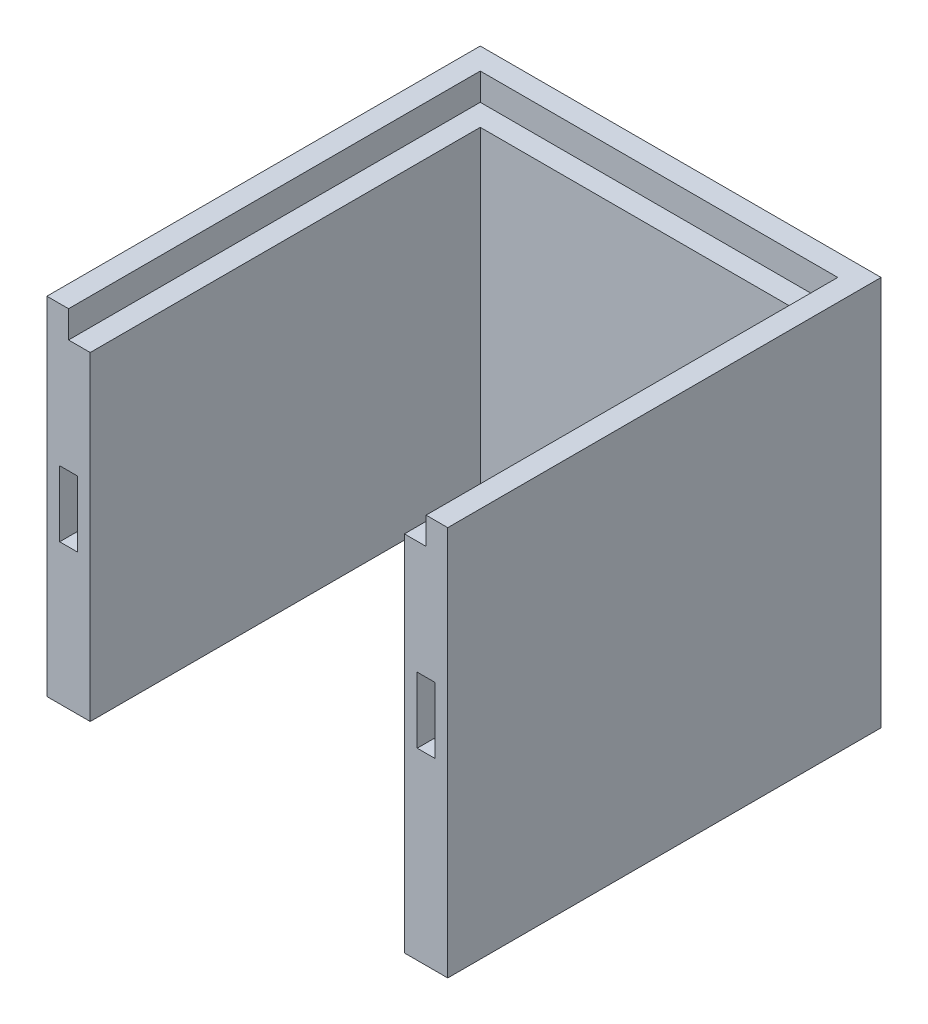
SolidWorks part; units mm, degrees
ref_plane "Front Plane" through (0, 0, 0) normal (0, 0, 1) x (1, 0, 0)
ref_plane "Top Plane" through (0, 0, 0) normal (0, 1, 0) x (1, 0, 0)
ref_plane "Right Plane" through (0, 0, 0) normal (1, 0, 0) x (0, 0, -1)
sketch "Sketch1" plane through (0, 0, 0) normal (0, 0, 1) x (1, 0, 0)
  line L1 (0, 0) -> (185, 0)
  line L2 (0, 0) -> (0, 160)
  line L3 (0, 160) -> (185, 160)
  line L4 (185, 0) -> (185, 160)
  dimension "D1" = 185
  dimension "D2" = 160
extrude "Boss-Extrude1" add sketch "Sketch1" along normal blind 20
sketch "Sketch2" plane through (0, 0, 20) normal (0, 0, 1) x (1, 0, 0)
  line L0 (0, 0) -> (185, 0) construction
  line L1 (0, 160) -> (20, 160)
  line L2 (0, 160) -> (0, 0)
  line L3 (0, 0) -> (20, 0)
  line L4 (20, 160) -> (20, 0)
  line L5 (92.5, 160) -> (92.5, 0) construction
  line L6 (185, 160) -> (0, 160) construction
  line L7 (185, 0) -> (165, 0)
  line L8 (165, 160) -> (165, 0)
  line L9 (185, 160) -> (165, 160)
  line L10 (185, 160) -> (185, 0)
  dimension "D1" = 20
extrude "Boss-Extrude2" add sketch "Sketch2" along normal blind 180
sketch "Sketch3" plane through (0, 0, 0) normal (0, -1, 0) x (1, 0, 0)
  line L6 (185, 0) -> (165, 0)
  line L7 (185, 0) -> (185, 200)
  line L8 (185, 200) -> (165, 200)
  line L9 (165, 0) -> (165, 200)
sketch "Sketch4" plane through (0, 0, 0) normal (0, 0, -1) x (-1, 0, 0)
  line L0 (-92.5, -2.923) -> (-92.5, 156.2167) construction
  line L1 (-185, 0) -> (-185, 160) construction
  line L3 (0, 0) -> (-185, 0) construction
  line L4 (-117.5, 50) -> (-67.5, 50)
  line L5 (-117.5, 50) -> (-117.5, 0)
  line L6 (-117.5, 0) -> (-67.5, 0)
  line L7 (-67.5, 50) -> (-67.5, 0)
  line L8 (-117.5, 50) -> (-67.5, 0) construction
  line L9 (-117.5, 0) -> (-67.5, 50) construction
  point P4 (-92.5, 25)
  dimension "D1" = 92.5
  dimension "D2" = 50
  dimension "D3" = 50
extrude "Cut-Extrude1" cut sketch "Sketch4" against normal through all
extrude "Boss-Extrude3" add sketch "Sketch3" along normal blind 20
fillet "Fillet1" radius 5 5 edges at (165, 0, 10) (117.5, 0, 10) (67.5, 0, 10) (117.5, 50, 10) (67.5, 50, 10)
sketch "Sketch6" plane through (0, 0, 200) normal (0, 0, 1) x (1, 0, 0)
  line L0 (20, 160) -> (0, 160) construction
  line L1 (5.9, 64.8) -> (14.1, 64.8)
  line L2 (5.9, 64.8) -> (5.9, 95.2)
  line L3 (5.9, 95.2) -> (14.1, 95.2)
  line L4 (14.1, 64.8) -> (14.1, 95.2)
  line L5 (5.9, 64.8) -> (14.1, 95.2) construction
  line L6 (5.9, 95.2) -> (14.1, 64.8) construction
  line L7 (0, 160) -> (0, 0) construction
  point P0 (10, 80)
  dimension "D1" = 64.8
  dimension "D2" = 10
  dimension "D3" = 8.2
  dimension "D4" = 30.4
extrude "Cut-Extrude2" cut sketch "Sketch6" against normal blind 12.5
fillet "Fillet2" radius 5 2 edges at (10, 64.8, 187.5) (10, 95.2, 187.5)
ref_plane "Plane1" through (92.5, 0, 0) normal (1, 0, 0) x (0, 0, -1)
mirror "Mirror1" about plane through (92.5, 0, 0) normal (1, 0, 0) of "Cut-Extrude2", "Fillet2"
sketch "Sketch7" plane through (0, 160, 0) normal (0, 1, 0) x (1, 0, 0)
  line L0 (20, -200) -> (0, -200) construction
  line L1 (10, -200) -> (175, -200)
  line L2 (10, -200) -> (10, -10)
  line L3 (10, -10) -> (175, -10)
  line L4 (175, -200) -> (175, -10)
  line L5 (185, 0) -> (0, 0) construction
  line L6 (185, -200) -> (185, 0) construction
  dimension "D1" = 10
  dimension "D2" = 10
extrude "Cut-Extrude3" cut sketch "Sketch7" against normal blind 12.5
